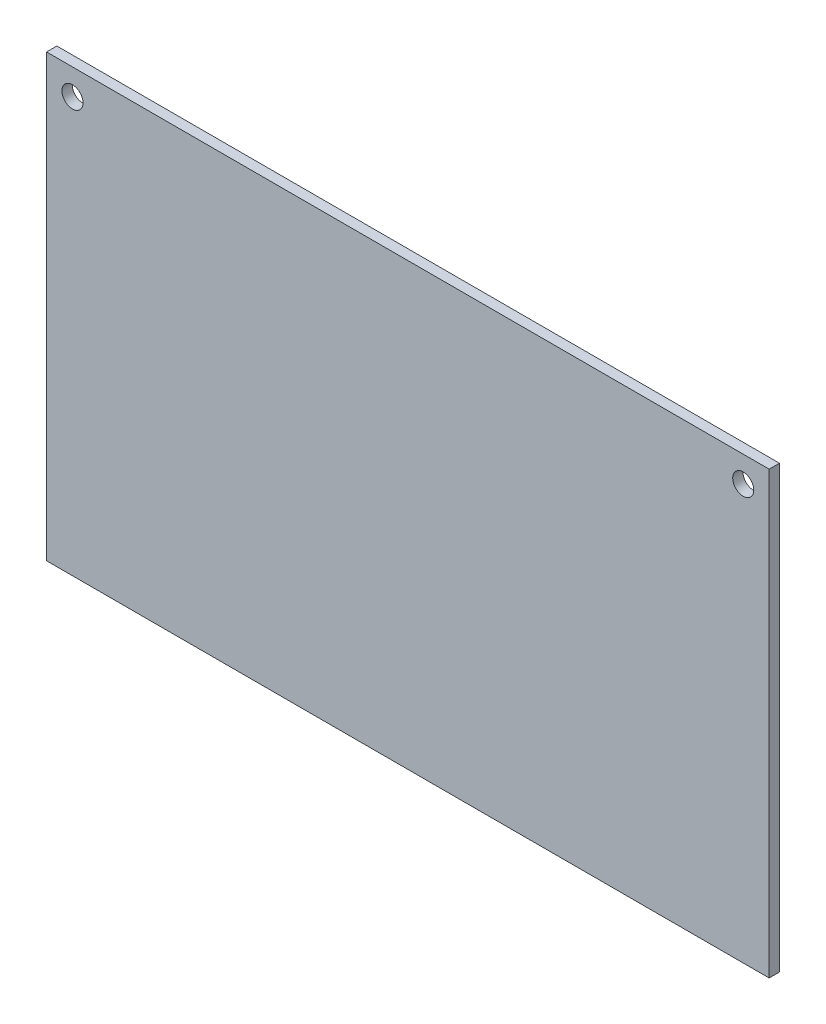
SolidWorks part; units mm, degrees
ref_plane "Front Plane" through (0, 0, 0) normal (0, 0, 1) x (1, 0, 0)
ref_plane "Top Plane" through (0, 0, 0) normal (0, 1, 0) x (1, 0, 0)
ref_plane "Right Plane" through (0, 0, 0) normal (1, 0, 0) x (0, 0, -1)
sketch "Sketch1" plane through (0, 0, 0) normal (0, 0, 1) x (1, 0, 0)
  line L1 (0, 0) -> (111.5, 0)
  line L2 (0, 0) -> (0, 68)
  line L3 (0, 68) -> (111.5, 68)
  line L4 (111.5, 0) -> (111.5, 68)
  circle A0 centre (4, 64) radius 1.6256
  circle A1 centre (107.5, 64) radius 1.6256
extrude "Boss-Extrude1" add sketch "Sketch1" along normal blind 1.5875
sketch "Sketch4" plane through (0, 0, 1.5875) normal (0, 0, 1) x (1, 0, 0)
  point P0 (0, 0.5)
  point P1 (-15.3167, 23.2132)
  point P5 (28, 0.5)
  point P6 (56, 0.5)
  point P7 (84, 0.5)
  point P8 (0, 28.5)
  point P9 (28, 28.5)
  point P10 (56, 28.5)
  point P11 (84, 28.5)
  dimension "D1" = 4
  dimension "D2" = 2
